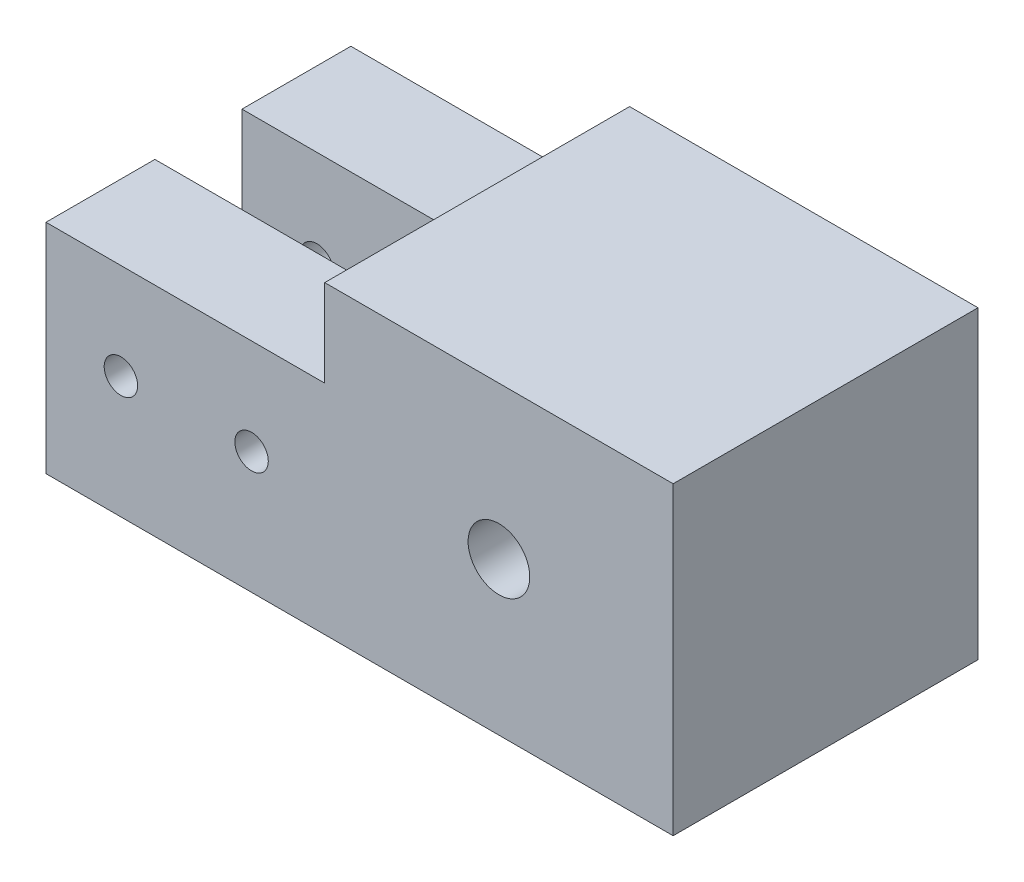
SolidWorks part; units mm, degrees
material "Plain Carbon Steel"
ref_plane "Front Plane" through (0, 0, 0) normal (0, 0, 1) x (1, 0, 0)
ref_plane "Top Plane" through (0, 0, 0) normal (0, 1, 0) x (1, 0, 0)
ref_plane "Right Plane" through (0, 0, 0) normal (1, 0, 0) x (0, 0, -1)
sketch "Sketch1" plane through (0, 0, 0) normal (1, 0, 0) x (0, 0, -1)
  line L1 (11.1125, 11.1125) -> (-11.1125, 11.1125)
  line L2 (11.1125, 11.1125) -> (11.1125, -11.1125)
  line L3 (11.1125, -11.1125) -> (-11.1125, -11.1125)
  line L4 (-11.1125, 11.1125) -> (-11.1125, -11.1125)
  line L5 (11.1125, 11.1125) -> (-11.1125, -11.1125) construction
  line L6 (11.1125, -11.1125) -> (-11.1125, 11.1125) construction
  point P0 (0, 0)
  dimension "D1" = 22.225
  dimension "D2" = 22.225
extrude "Boss-Extrude1" add sketch "Sketch1" along normal blind 25.4
hole_wizard "#8 Clearance Hole1" positions "3DSketch1" profile "Sketch2" hole size "#8" standard "ANSI Inch" end condition through all
sketch3d "3DSketch1"
  line L0 (25.4, 11.1125, 11.1125) -> (0, 11.1125, 11.1125) construction
  line L10 (0, 11.1125, 11.1125) -> (0, -11.1125, 11.1125)
  line L11 (0, -11.1125, 11.1125) -> (25.4, -11.1125, 11.1125)
  line L12 (25.4, -11.1125, 11.1125) -> (25.4, 11.1125, 11.1125)
  line L13 (25.4, 11.1125, 11.1125) -> (0, 11.1125, 11.1125)
  line L14 (0, 11.1125, 11.1125) -> (0, -11.1125, 11.1125)
  line L15 (0, -11.1125, 11.1125) -> (25.4, -11.1125, 11.1125)
  line L16 (25.4, -11.1125, 11.1125) -> (25.4, 11.1125, 11.1125)
  line L17 (25.4, 11.1125, 11.1125) -> (0, 11.1125, 11.1125)
  point P0 (12.7, 0, 11.1125)
  dimension "D1" = 11.1125
  dimension "D2" = 0
  dimension "D3" = 22.225
  dimension "D4" = 25.4
  dimension "D5" = 12.7
sketch "Sketch2" plane through (12.7, 0, 11.1125) normal (1, 0, 0) x (0, -1, 0)
  line L0 (0, 0) -> (0, 22.225)
  line L1 (0, 22.225) -> (2.2479, 22.225)
  line L2 (2.2479, 22.225) -> (2.2479, 0)
  line L5 (2.2479, 0) -> (0, 0)
  line L11 (0, -6.35) -> (0, 107.95) construction
  dimension "Thru Hole Dia." = 4.4958
  dimension "Thru Hole Depth" = 22.225
sketch "Sketch3" plane through (0, 0, 0) normal (-1, 0, 0) x (0, 0, 1)
  line L1 (-3.175, -4.7625) -> (3.175, -4.7625)
  line L2 (-3.175, -4.7625) -> (-3.175, 4.7625)
  line L3 (-3.175, 4.7625) -> (3.175, 4.7625)
  line L4 (3.175, -4.7625) -> (3.175, 4.7625)
  line L5 (-3.175, -4.7625) -> (3.175, 4.7625) construction
  line L6 (-3.175, 4.7625) -> (3.175, -4.7625) construction
  line L7 (-3.175, 4.7625) -> (-11.1125, 4.7625)
  line L8 (-3.175, 4.7625) -> (-3.175, -11.1125)
  line L9 (-3.175, -11.1125) -> (-11.1125, -11.1125)
  line L10 (-11.1125, 4.7625) -> (-11.1125, -11.1125)
  line L11 (3.175, 4.7625) -> (11.1125, 4.7625)
  line L12 (3.175, 4.7625) -> (3.175, -11.1125)
  line L13 (3.175, -11.1125) -> (11.1125, -11.1125)
  line L14 (11.1125, 4.7625) -> (11.1125, -11.1125)
  point P0 (0, 0)
  line M1 (11.1125, -11.1125) -> (11.1125, 11.1125)
  line M3 (-11.1125, 11.1125) -> (-11.1125, -11.1125)
  line M4 (-11.1125, -11.1125) -> (11.1125, -11.1125)
  dimension "D1" = 9.525
  dimension "D2" = 6.35
extrude "Boss-Extrude2" add sketch "Sketch3" along normal blind 20.32 contours L8 L2 L7 M3 M4 | L4 L12 L11 M4 M1
hole_wizard "#2 Clearance Hole1" positions "Sketch5" profile "Sketch6" hole size "#2" standard "ANSI Inch" end condition through all
sketch "Sketch5" plane through (0, 0, -11.1125) normal (0, 0, -1) x (-1, 0, 0)
  line L12 (-25.4, -11.1125) -> (20.32, -11.1125)
  line L13 (20.32, -11.1125) -> (20.32, 4.7625)
  line L14 (20.32, 4.7625) -> (0, 4.7625)
  line L15 (0, 4.7625) -> (0, 11.1125)
  line L16 (0, 11.1125) -> (-25.4, 11.1125)
  line L17 (-25.4, 11.1125) -> (-25.4, -11.1125)
  line L18 (-25.4, -11.1125) -> (20.32, -11.1125)
  line L19 (20.32, -11.1125) -> (20.32, 4.7625)
  line L20 (20.32, 4.7625) -> (0, 4.7625)
  line L21 (0, 4.7625) -> (0, 11.1125)
  line L22 (0, 11.1125) -> (-25.4, 11.1125)
  line L23 (-25.4, 11.1125) -> (-25.4, -11.1125)
  point P0 (5.334, -2.2225)
  point P2 (14.859, -2.2225)
  dimension "D2" = 5.334
  dimension "D3" = 9.525
  dimension "D4" = 6.985
  dimension "D5" = 6.985
  dimension "D1" = 0
sketch "Sketch6" plane through (-5.334, -2.2225, -11.1125) normal (1, 0, 0) x (0, 1, 0)
  line L0 (0, 0) -> (0, 22.225)
  line L1 (0, 22.225) -> (1.2192, 22.225)
  line L2 (1.2192, 22.225) -> (1.2192, 0)
  line L5 (1.2192, 0) -> (0, 0)
  line L11 (0, -6.35) -> (0, 107.95) construction
  dimension "Thru Hole Dia." = 2.4384
  dimension "Thru Hole Depth" = 22.225
equation "\"D1@3DSketch1\"=\"D3@3DSketch1\"/2"
equation "\"D5@3DSketch1\"=\"D4@3DSketch1\"/2"
